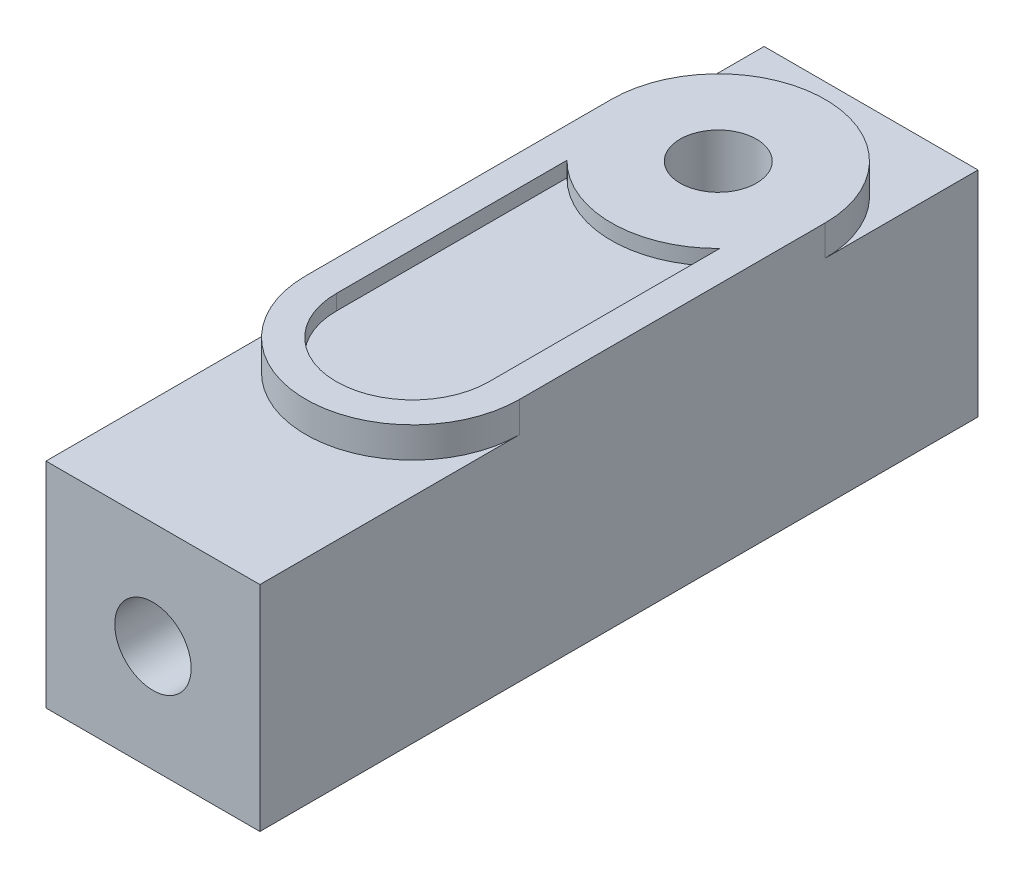
SolidWorks part; units mm, degrees
ref_plane "Plane1" through (0, 0, 0) normal (0, 0, 1) x (1, 0, 0)
ref_plane "Plane2" through (0, 0, 0) normal (0, 1, 0) x (1, 0, 0)
ref_plane "Plane3" through (0, 0, 0) normal (1, 0, 0) x (0, 0, -1)
sketch "Esquisse1" plane through (0, 0, 0) normal (0, 0, 1) x (1, 0, 0)
  line L1 (0, 0) -> (7, 0)
  line L2 (0, 0) -> (0, 7)
  line L3 (0, 7) -> (7, 7)
  line L4 (7, 0) -> (7, 7)
  dimension "D1" = 7
  dimension "D2" = 7
extrude "Base-Extrusion" add sketch "Esquisse1" along normal blind 23.5
sketch "Esquisse2" plane through (0, 7, 0) normal (0, 1, 0) x (-1, 0, 0)
  line L2 (-3.5, 5) -> (0, 5) construction
  line L3 (-3.5, 5) -> (-11, 5) construction
  line L4 (-3.5, 5) -> (-3.5, 15) construction
  line L5 (-3.5, 15) -> (-10, 15) construction
  line L6 (-3.5, 15) -> (-1, 15) construction
  line L7 (0, 5) -> (0, 15)
  line L8 (-7, 5) -> (-7, 15)
  line L9 (-7, 23.5) -> (-7, 0) construction
  arc A0 (-7, 5) -> (0, 5) centre (-3.5, 5) ccw
  arc A1 (0, 15) -> (-7, 15) centre (-3.5, 15) ccw
  point P5 (-7, 11.75)
  dimension "D3" = 3.5
  dimension "D1" = 3.5
  dimension "D2" = 7
extrude "Boss.-Extru.1" add sketch "Esquisse2" along normal blind 1
sketch "Esquisse3" plane through (0, 8, 0) normal (0, 1, 0) x (-1, 0, 0)
  circle A0 centre (-3.5, 5) radius 1.25
  dimension "D1" = 2.5
extrude "Enlèv. mat.-Extru.1" cut sketch "Esquisse3" against normal through all
sketch "Esquisse4" plane through (0, 8, 0) normal (0, 1, 0) x (-1, 0, 0)
  line L0 (-3.5, 15) -> (1, 15) construction
  line L1 (-3.5, 15) -> (-11, 15) construction
  line L2 (-1, 15) -> (-1, 7.4495)
  line L3 (-6, 15) -> (-6, 7.4495)
  arc A0 (-1, 7.4495) -> (-6, 7.4495) centre (-3.5, 5) ccw
  arc A1 (-1, 15) -> (-6, 15) centre (-3.5, 15) ccw
  dimension "D1" = 5
extrude "Enlèv. mat.-Extru.2" cut sketch "Esquisse4" against normal blind 0.5
sketch "Esquisse5" plane through (0, 0, 23.5) normal (0, 0, 1) x (1, 0, 0)
  line L0 (0, 7) -> (7, 0) construction
  circle A0 centre (3.5, 3.5) radius 1.25
  dimension "D1" = 2.5
extrude "Enlèv. mat.-Extru.3" cut sketch "Esquisse5" against normal blind 10
